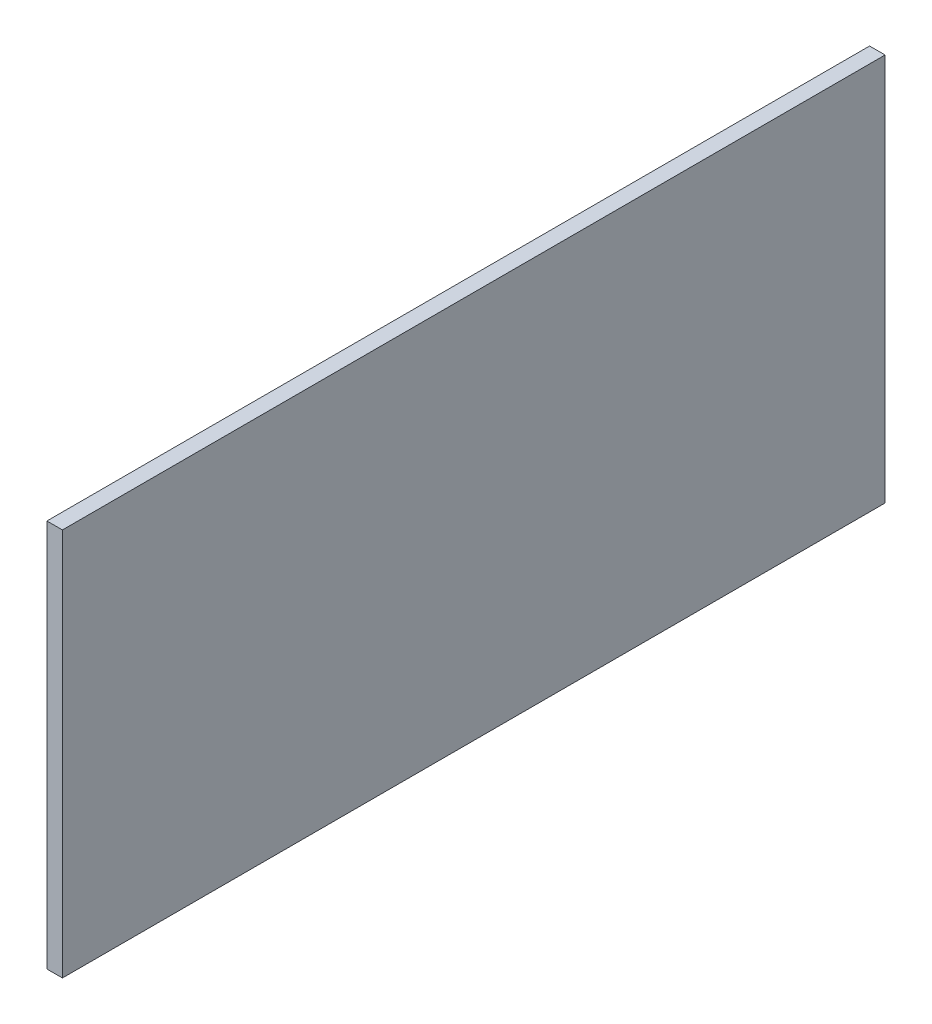
SolidWorks part; units mm, degrees
ref_plane "Front Plane" through (0, 0, 0) normal (0, 0, 1) x (1, 0, 0)
ref_plane "Top Plane" through (0, 0, 0) normal (0, 1, 0) x (1, 0, 0)
ref_plane "Right Plane" through (0, 0, 0) normal (1, 0, 0) x (0, 0, -1)
sketch "Croquis1" plane through (0, 0, 0) normal (1, 0, 0) x (0, 0, -1)
  line L1 (-79.505, 37.5) -> (79.505, 37.5)
  line L2 (-79.505, 37.5) -> (-79.505, -37.5)
  line L3 (-79.505, -37.5) -> (79.505, -37.5)
  line L4 (79.505, 37.5) -> (79.505, -37.5)
  line L5 (-79.505, 37.5) -> (79.505, -37.5) construction
  line L6 (-79.505, -37.5) -> (79.505, 37.5) construction
  point P0 (0, 0)
  dimension "D1" = 75
  dimension "D2" = 159.01
extrude "Saliente-Extruir1" add sketch "Croquis1" along normal blind 3
